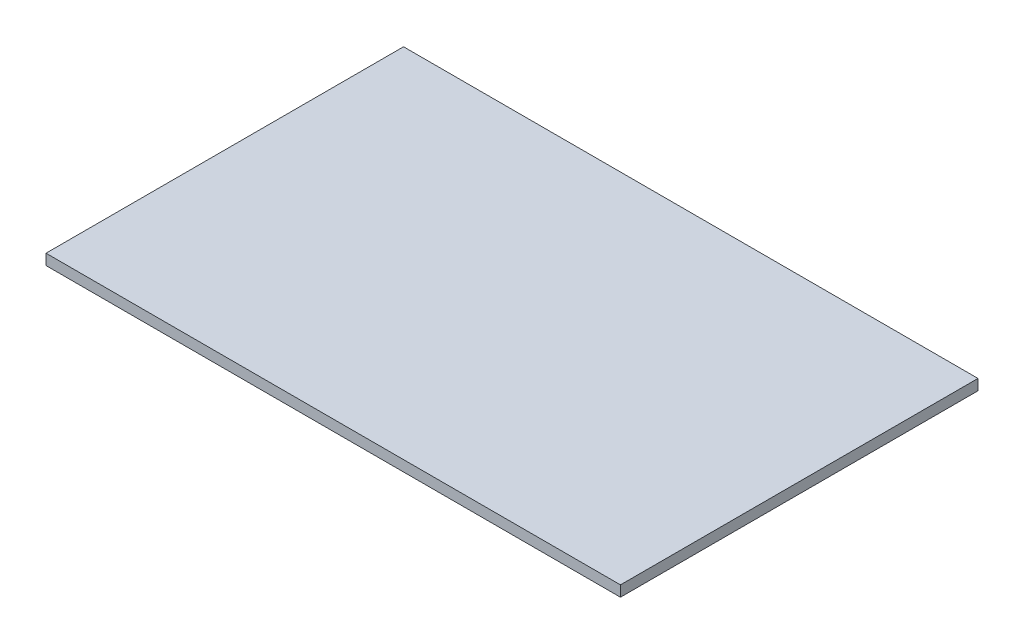
SolidWorks part; units mm, degrees
ref_plane "Спереди" through (0, 0, 0) normal (0, 0, 1) x (1, 0, 0)
ref_plane "Сверху" through (0, 0, 0) normal (0, 1, 0) x (1, 0, 0)
ref_plane "Справа" through (0, 0, 0) normal (1, 0, 0) x (0, 0, -1)
sketch "Эскиз1" plane through (0, 0, 0) normal (0, 1, 0) x (1, 0, 0)
  line L1 (0, 0) -> (964, 0)
  line L2 (0, 0) -> (0, 600)
  line L3 (0, 600) -> (964, 600)
  line L4 (964, 0) -> (964, 600)
  dimension "D1" = 600
  dimension "D2" = 964
extrude "Бобышка-Вытянуть1" add sketch "Эскиз1" along normal blind 18
